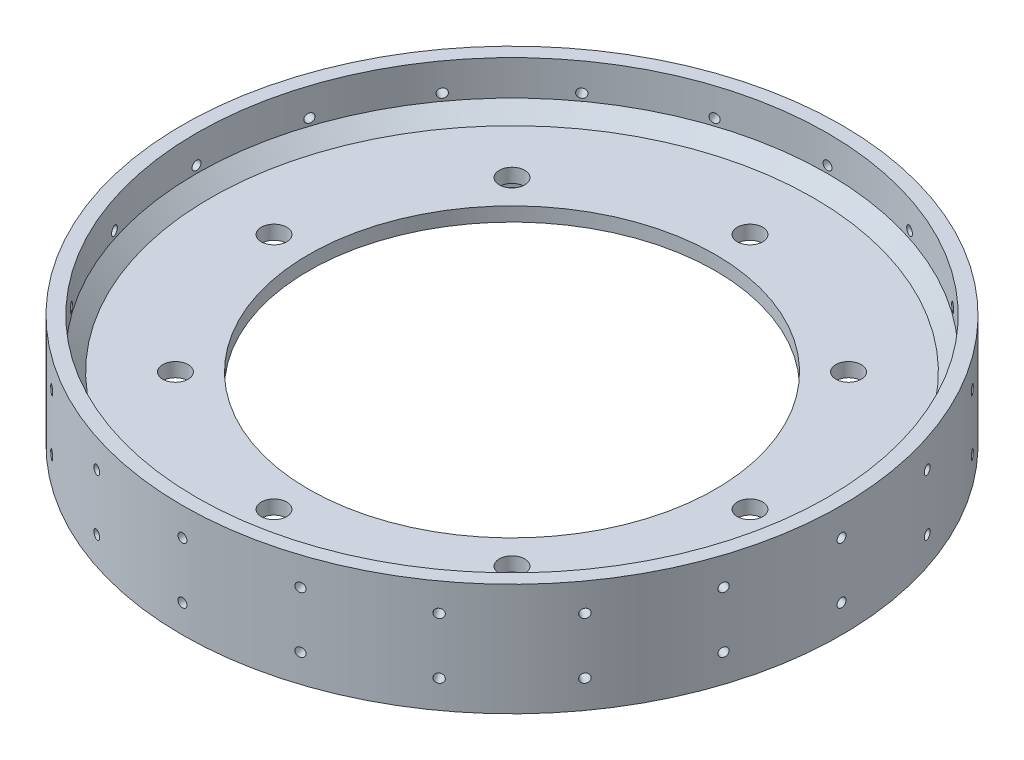
SolidWorks part; units mm, degrees
material "6061-T6 (SS)"
ref_plane "Front Plane" through (0, 0, 0) normal (0, 0, 1) x (1, 0, 0)
ref_plane "Top Plane" through (0, 0, 0) normal (0, 1, 0) x (1, 0, 0)
ref_plane "Right Plane" through (0, 0, 0) normal (1, 0, 0) x (0, 0, -1)
sketch "Sketch1" plane through (0, 0, 0) normal (0, 0, 1) x (1, 0, 0)
  line L0 (142.875, 0) -> (149.225, 0)
  line L1 (149.225, 0) -> (149.225, 50.8)
  line L2 (149.225, 50.8) -> (142.875, 50.8)
  line L3 (142.875, 50.8) -> (142.875, 28.575)
  line L4 (142.875, 28.575) -> (92.075, 28.575)
  line L5 (92.075, 28.575) -> (92.075, 22.225)
  line L6 (92.075, 22.225) -> (142.875, 22.225)
  line L7 (142.875, 22.225) -> (142.875, 0)
  line L8 (0, 48.7938) -> (0, -58.7251) construction
  dimension "D1" = 6.35
  dimension "D2" = 50.8
  dimension "D3" = 50.8
  dimension "D4" = 6.35
  dimension "D5" = 22.225
  dimension "D6" = 149.225
revolve "Revolve1" add sketch "Sketch1" angle 360 about L8
chamfer "Chamfer1" distance 6.35 angle 45 2 edges at (0, 22.225, 142.875) (0, 28.575, 142.875)
sketch "Sketch2" plane through (0, 28.575, 0) normal (0, 1, 0) x (1, 0, 0)
  line L0 (0, 157.7728) -> (0, -198.3593) construction
  line L1 (-197.9429, 0) -> (209.299, 0) construction
  line L2 (-160.3937, 160.3937) -> (184.6724, -184.6724) construction
  line L3 (150.3007, 150.3007) -> (-158.9798, -158.9798) construction
  line L4 (-217.4143, 109.6513) -> (120.8881, -228.6512) construction
  line L5 (-58.11, 165.8731) -> (230.0704, -122.3073) construction
  line L6 (177.8915, 70.1284) -> (-70.7462, -178.5093) construction
  line L7 (51.5519, 159.315) -> (-187.8494, -80.0863) construction
  point P5 (-76.2, 76.2)
  point P6 (76.2, 76.2)
  point P7 (76.2, -76.2)
  point P8 (-76.2, -76.2)
  point P9 (107.7631, 0)
  point P10 (0, -107.7631)
  point P11 (0, 107.7631)
  point P15 (-107.7631, 0)
  point P25 (0, 0)
  point P26 (0, 0)
  point P27 (0, 0)
  point P28 (0, 0)
  point P29 (0, 0)
  dimension "D1" = 152.4
  dimension "D2" = 152.4
  dimension "D3" = 76.2
  dimension "D4" = 76.2
  dimension "D5" = 45
  dimension "D6" = 45
  dimension "D7" = 152.4
  dimension "D8" = 76.2
  dimension "D9" = 152.4
  dimension "D10" = 76.2
hole_wizard "1/2-20 Tapped Hole2" positions "3DSketch2" profile "Sketch4" tap size "1/2-20" standard "ANSI Inch" end condition up to next
sketch3d "3DSketch2"
  line L0 (-160.3937, 28.575, -160.3937) -> (184.6724, 28.575, 184.6724) construction
  point P0 (0, 28.575, 107.7631)
  point P3 (-76.2, 28.575, 76.2)
  point P6 (-107.7631, 28.575, 0)
  point P9 (76.2, 28.575, 76.2)
  point P12 (107.7631, 28.575, 0)
  point P15 (76.2, 28.575, -76.2)
  point P18 (0, 28.575, -107.7631)
  point P21 (-76.2, 28.575, -76.2)
  point P26 (-76.2, 28.575, -76.2)
sketch "Sketch4" plane through (0, 28.575, 107.7631) normal (1, 0, 0) x (0, 0, 1)
  line L0 (0, 0) -> (0, 6.35)
  line L1 (0, 6.35) -> (5.7544, 6.35)
  line L2 (5.7544, 6.35) -> (5.7544, 0)
  line L5 (5.7544, 0) -> (0, 0)
  line L11 (0, -6.35) -> (0, 107.95) construction
  dimension "Thru Tap Drill Dia." = 11.5087
  dimension "Thru Tap Drill Depth" = 6.35
cosmetic thread "Hole Thread5" parameters "D2"=12.7
cosmetic thread "Hole Thread6" parameters "D2"=12.7
cosmetic thread "Hole Thread7" parameters "D2"=12.7
cosmetic thread "Hole Thread8" parameters "D2"=12.7
cosmetic thread "Hole Thread9" parameters "D2"=12.7
cosmetic thread "Hole Thread10" parameters "D2"=12.7
cosmetic thread "Hole Thread11" parameters "D2"=12.7
cosmetic thread "Hole Thread12" parameters "D2"=12.7
ref_plane "Plane1" through (149.225, 0, 0) normal (1, 0, 0) x (0, 0, -1)
sketch "Sketch5" plane through (149.225, 0, 0) normal (1, 0, 0) x (0, 0, -1)
  line L0 (0, 69.697) -> (0, -26.2977) construction
  line L1 (-142.875, 0) -> (142.875, 0) construction
  line L2 (149.225, 50.8) -> (-149.225, 50.8) construction
  line L3 (-142.875, 0) -> (142.875, 0) construction
  line L4 (149.225, 50.8) -> (-149.225, 50.8) construction
hole_wizard "#10-32 Tapped Hole1" positions "3DSketch3" profile "Sketch6" tap size "#10-32" standard "ANSI Inch"
sketch3d "3DSketch3"
  line L0 (149.225, 69.697, 0) -> (149.225, -26.2977, 0) construction
  line L1 (149.225, 0, 142.875) -> (149.225, 0, -142.875) construction
  line L2 (149.225, 50.8, -149.225) -> (149.225, 50.8, 149.225) construction
  point P0 (149.225, 12.7, 0)
  point P2 (149.225, 38.1, 0)
  point P6 (146.05, 39.9144, 0)
  point P9 (146.05, 10.3326, 0)
  dimension "D1" = 12.7
  dimension "D2" = 12.7
sketch "Sketch6" plane through (149.225, 12.7, 0) normal (0, 1, 0) x (0, 0, -1)
  line L0 (0, 0) -> (0, 329.2593)
  line L1 (0, 329.2593) -> (2.0193, 329.2593)
  line L2 (2.0193, 329.2593) -> (2.0193, 0)
  line L5 (2.0193, 0) -> (0, 0)
  line L11 (0, -6.35) -> (0, 107.95) construction
  dimension "Thru Tap Drill Dia." = 4.0386
  dimension "Thru Tap Drill Depth" = 329.2593
cosmetic thread "Hole Thread13" parameters "D2"=4.826
cosmetic thread "Hole Thread14" parameters "D2"=4.826
pattern_circular "CirPattern1" count 20 over 360 about axis through (0, 48.7938, 0) along (0, 1, 0) of "#10-32 Tapped Hole1"
equation "\"D5@Sketch1\"=(\"D2@Sketch1\"-\"D4@Sketch1\")/2"
equation "\"D2@Sketch2\"=\"D1@Sketch2\""
equation "\"D3@Sketch2\"=\"D2@Sketch2\"/2"
equation "\"D4@Sketch2\"=\"D3@Sketch2\""
equation "\"D8@Sketch2\"=\"D7@Sketch2\"/2"
equation "\"D10@Sketch2\"=\"D9@Sketch2\"/2"
